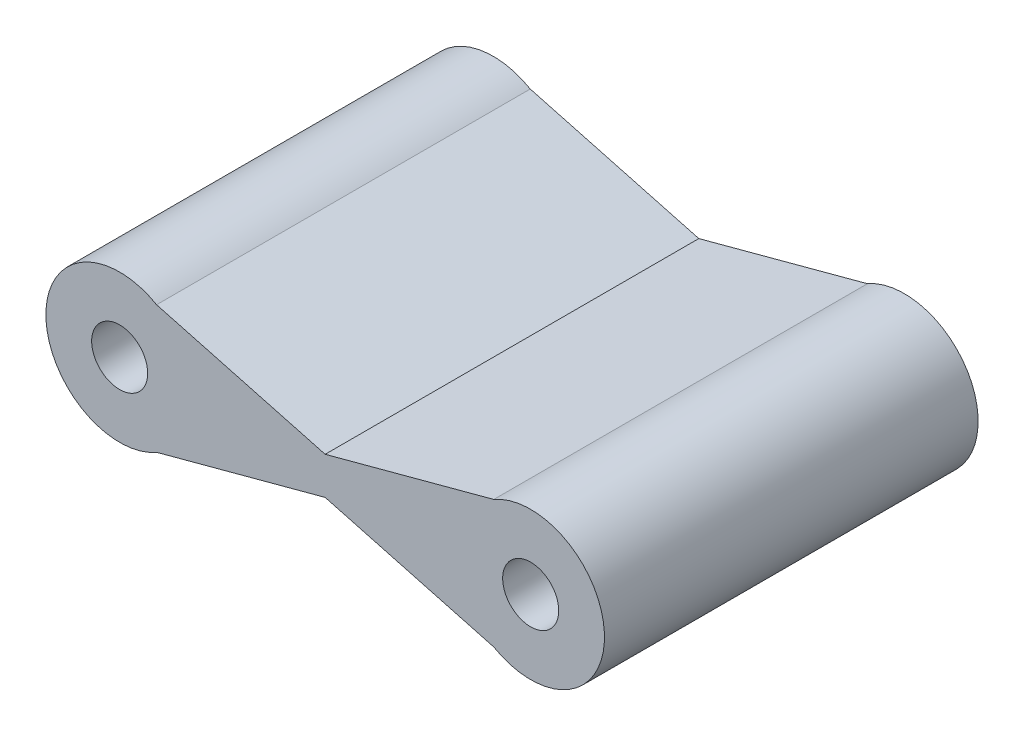
SolidWorks part; units mm, degrees
ref_plane "Front Plane" through (0, 0, 0) normal (0, 0, 1) x (1, 0, 0)
ref_plane "Top Plane" through (0, 0, 0) normal (0, 1, 0) x (1, 0, 0)
ref_plane "Right Plane" through (0, 0, 0) normal (1, 0, 0) x (0, 0, -1)
sketch "Sketch1" plane through (0, 0, 0) normal (0, 0, 1) x (1, 0, 0)
  line L0 (0, 2.475) -> (5.5, 1)
  line L1 (0, 1) -> (11, 1)
  line L2 (0, 1) -> (0, 0)
  line L3 (0, 0) -> (11, 0)
  line L4 (11, 1) -> (11, 0)
  line L5 (5.5, 1) -> (11, 2.475)
  line L6 (11, -1.475) -> (5.5, 0)
  line L7 (0, -1.475) -> (5.5, 0)
  circle A0 centre (0, 0.5) radius 1.975
  circle A1 centre (11, 0.5) radius 1.975
  circle A2 centre (0, 0.5) radius 0.75
  circle A3 centre (11, 0.5) radius 0.75
  dimension "D3" = 3.95
  dimension "D4" = 1.5
  dimension "D1" = 1
  dimension "D2" = 11
extrude "Boss-Extrude1" add sketch "Sketch1" along normal blind 10 contours L1 A0 L0 L7 L3 L2 | L3 A0 L1 L2 | A1 L1 A0 L3 | A0 L1 L0 | A1 L5 L1 | L5 A1 L1 L4 L3 L6 | L1 A1 L3 L4 | A1 L3 L6 | A0 L7 L3 | L5 A1 | L6 A1 | L7 A0 | L0 A0
